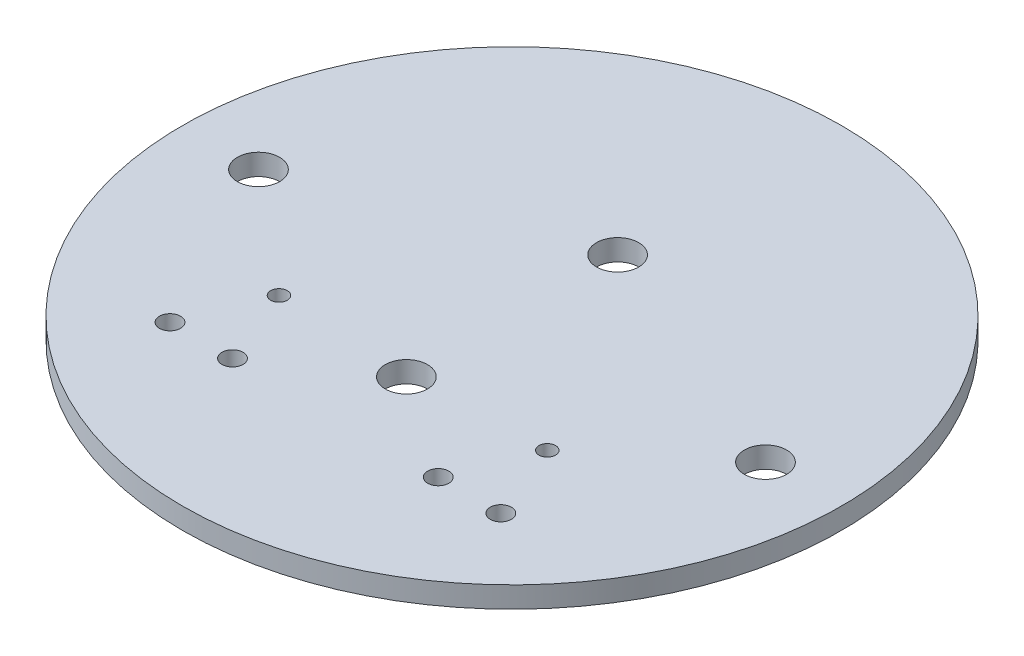
SolidWorks part; units mm, degrees
ref_plane "Front Plane" through (0, 0, 0) normal (0, 0, 1) x (1, 0, 0)
ref_plane "Top Plane" through (0, 0, 0) normal (0, 1, 0) x (1, 0, 0)
ref_plane "Right Plane" through (0, 0, 0) normal (1, 0, 0) x (0, 0, -1)
sketch "Sketch1" plane through (0, 0, 0) normal (0, 1, 0) x (1, 0, 0)
  circle A0 centre (0, 0) radius 49.53
  dimension "D1" = 99.06
extrude "Boss-Extrude1" add sketch "Sketch1" along normal blind 3.175
extrude "Cut-Extrude1" cut sketch "Sketch2" against normal blind 263.398
sketch "Sketch2" plane through (-55.0397, 234.95, -116.0884) normal (0, 1, 0) x (-1, 0, 0)
  circle A0 centre (-93.1397, 116.0884) radius 3.175
  circle A1 centre (-16.9397, 116.0884) radius 3.175
extrude "Cut-Extrude2" cut sketch "Sketch3" against normal blind 25.4
sketch "Sketch3" plane through (-28.2644, 0, -82.3713) normal (0, -1, 0) x (1, 0, 0)
  circle A0 centre (28.2644, 98.2463) radius 3.175
  circle A1 centre (28.2644, 66.4963) radius 3.175
extrude "Cut-Extrude3" cut sketch "Sketch4" against normal blind 50.8
sketch "Sketch4" plane through (-28.2644, 0, -82.3713) normal (0, -1, 0) x (-1, 0, 0)
  circle A0 centre (-3.4041, -108.9143) radius 1.5875
  circle A1 centre (-12.8021, -108.9143) radius 1.5875
  circle A2 centre (-43.7266, -108.9143) radius 1.5875
  circle A3 centre (-53.1246, -108.9143) radius 1.5875
  circle A4 centre (-8.1031, -97.2303) radius 1.25
  circle A5 centre (-48.4256, -97.2303) radius 1.25
  point P8 (-3.4041, -105.7393)
  point P9 (-12.8021, -105.7393)
  point P12 (-43.7266, -105.7393)
  point P15 (-53.1246, -105.7393)
